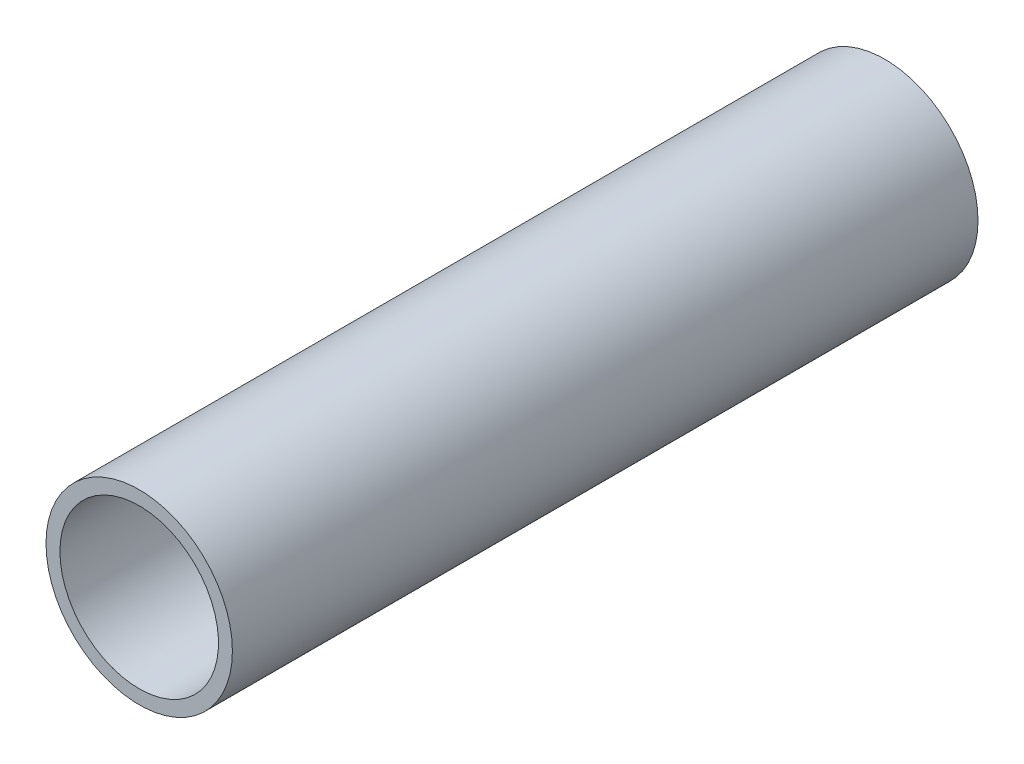
SolidWorks part; units mm, degrees
material "AISI 304"
ref_plane "Front Plane" through (0, 0, 0) normal (0, 0, 1) x (1, 0, 0)
ref_plane "Top Plane" through (0, 0, 0) normal (0, 1, 0) x (1, 0, 0)
ref_plane "Right Plane" through (0, 0, 0) normal (1, 0, 0) x (0, 0, -1)
sketch "Sketch1" plane through (0, 0, 0) normal (0, 0, 1) x (1, 0, 0)
  line L0 (-4.7625, 0) -> (4.7625, 0) construction
  line L1 (0, -4.7625) -> (0, 4.7625) construction
  circle A0 centre (0, 0) radius 4.7625
  circle A1 centre (0, 0) radius 4.0513
  point P4 (0, 0)
  point P9 (0, 0)
  point P10 (-4.0513, 0)
  dimension "ID" = 8.1026
  dimension "OD" = 9.525
  dimension "Wall Thickness" = 0.7112
sketch "Sketch2" plane through (0, 0, 0) normal (1, 0, 0) x (0, 0, -1)
  line L0 (19.05, 4.7625) -> (-19.05, 4.7625) construction
  line L1 (0, 4.7625) -> (0, -4.7625) construction
  point P3 (-9.525, 4.7625)
  point P4 (0, 4.7625)
  point P5 (9.525, 4.7625)
  dimension "Length" = 38.1
  dimension "D1" = 9.525
  dimension "D2" = 9.525
sketch "Sketch3" plane through (0, 0, 0) normal (0, 0, 1) x (1, 0, 0)
  line L0 (0, -4.7625) -> (0, 4.7625) construction
  circle A0 centre (0, 0) radius 4.7625
  circle A1 centre (0, 0) radius 4.0513
  circle A2 centre (0, 0) radius 4.0513 construction
extrude "Boss-Extrude1" add sketch "Sketch3" along normal mid plane 38.1
equation "\"D1@Boss-Extrude1\" = \"Length@Sketch2\""
equation "\"D1@Sketch2\"=\"OD@Sketch1\"*1"
equation "\"D2@Sketch2\"=\"D1@Sketch2\""
